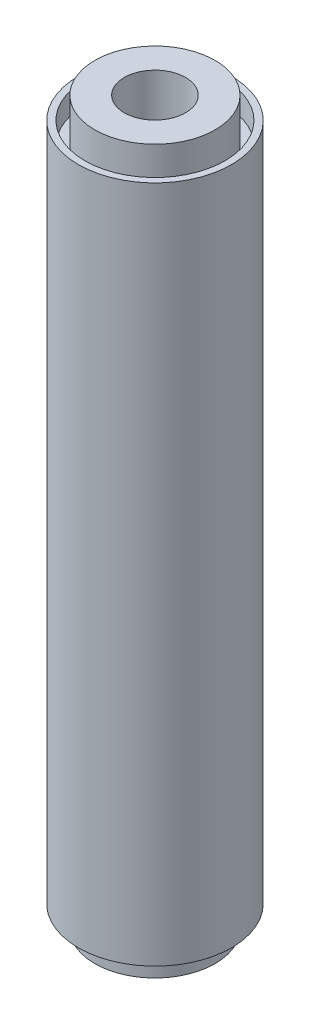
SolidWorks part; units mm, degrees
ref_plane "Front Plane" through (0, 0, 0) normal (0, 0, 1) x (1, 0, 0)
ref_plane "Top Plane" through (0, 0, 0) normal (0, 1, 0) x (1, 0, 0)
ref_plane "Right Plane" through (0, 0, 0) normal (1, 0, 0) x (0, 0, -1)
sketch "Sketch1" plane through (0, 0, 0) normal (0, 1, 0) x (1, 0, 0)
  circle A0 centre (0, 0) radius 44.45
  circle A1 centre (0, 0) radius 40.64
  dimension "D1" = 88.9
  dimension "D2" = 81.28
extrude "Boss-Extrude1" add sketch "Sketch1" along normal blind 393.7
ref_plane "refPlane_innerStop_TOP" through (0, 355.6, 0) normal (0, 1, 0) x (1, 0, 0)
sketch "Sketch3" plane through (0, 355.6, 0) normal (0, 1, 0) x (1, 0, 0)
  circle A0 centre (0, 0) radius 40.64
  dimension "D1" = 81.28
extrude "Boss-Extrude2" add sketch "Sketch3" along normal blind 25.4
sketch "Sketch4" plane through (0, 381, 0) normal (0, 1, 0) x (1, 0, 0)
  circle A0 centre (0, 0) radius 34.925
  dimension "D1" = 69.85
extrude "Boss-Extrude3" add sketch "Sketch4" along normal blind 25.4
ref_plane "refPlane_innerStop_BOTTOM" through (0, 38.1, 0) normal (0, -1, 0) x (-1, 0, 0)
sketch "Sketch6" plane through (0, 38.1, 0) normal (0, -1, 0) x (-1, 0, 0)
  circle A0 centre (0, 0) radius 40.64
  dimension "D1" = 81.28
extrude "Boss-Extrude4" add sketch "Sketch6" along normal blind 25.4
sketch "Sketch7" plane through (0, 12.7, 0) normal (0, -1, 0) x (1, 0, 0)
  circle A0 centre (0, 0) radius 34.925
  dimension "D1" = 69.85
extrude "Boss-Extrude5" add sketch "Sketch7" along normal blind 25.4
sketch "Sketch9" plane through (0, 406.4, 0) normal (0, 1, 0) x (1, 0, 0)
  circle A0 centre (0, 0) radius 17.78
  dimension "D1" = 35.56
extrude "Cut-Extrude1" cut sketch "Sketch9" against normal blind 152.4
